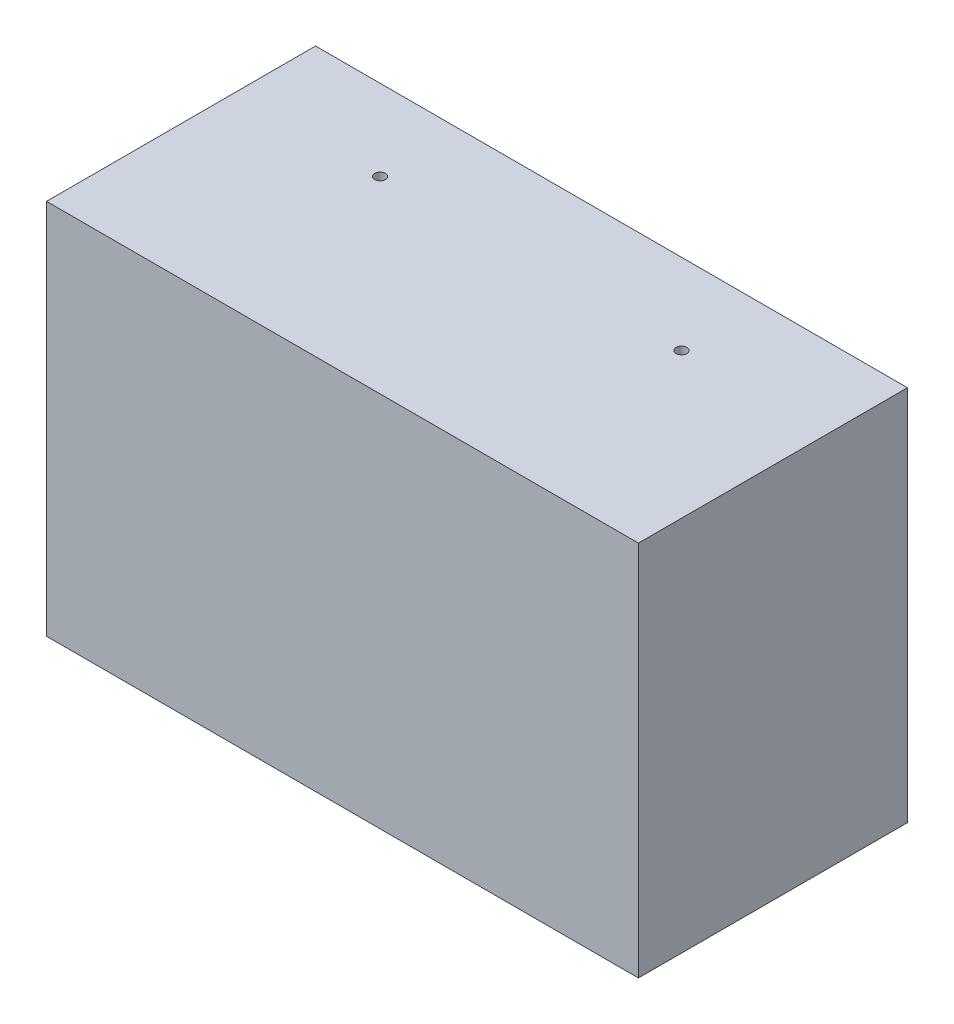
SolidWorks part; units mm, degrees
ref_plane "前基準面" through (0, 0, 0) normal (0, 0, 1) x (1, 0, 0)
ref_plane "上基準面" through (0, 0, 0) normal (0, 1, 0) x (1, 0, 0)
ref_plane "右基準面" through (0, 0, 0) normal (1, 0, 0) x (0, 0, -1)
sketch "草圖1" plane through (0, 0, 0) normal (0, 0, 1) x (1, 0, 0)
  line L0 (-102.947, 0) -> (115.7948, 0) construction
  line L1 (0, 64.9755) -> (0, -71.8056) construction
  line L3 (-55, 35) -> (55, 35)
  line L4 (-55, 35) -> (-55, -35)
  line L5 (-55, -35) -> (55, -35)
  line L6 (55, 35) -> (55, -35)
  dimension "D1" = 110
  dimension "D2" = 70
  dimension "D3" = 35
  dimension "D4" = 55
extrude "填料-伸長1" add sketch "草圖1" along normal blind 50
sketch "草圖3" plane through (0, 0, 0) normal (0, 0, 1) x (1, 0, 0)
  line L0 (0, 43.0067) -> (0, -45.1363) construction
  line L1 (63.4157, 0) -> (-65.1903, 0) construction
  line L3 (50, 30) -> (-50, 30)
  line L4 (50, 30) -> (50, -30)
  line L5 (50, -30) -> (-50, -30)
  line L6 (-50, 30) -> (-50, -30)
  dimension "D1" = 100
  dimension "D2" = 60
  dimension "D3" = 30
  dimension "D4" = 50
extrude "除料-伸長1" cut sketch "草圖3" along normal blind 35
sketch "草圖4" plane through (0, 0, 0) normal (0, 1, 0) x (1, 0, 0)
  line L0 (0, -68.6198) -> (0, 19.6124) construction
  line L1 (-69.152, -24.5037) -> (67.9388, -24.5037) construction
  line L2 (55, -50) -> (55, 0) construction
  line L3 (55, 0) -> (-55, 0) construction
  circle A0 centre (28, -15) radius 1
  circle A1 centre (-28, -15) radius 1
  dimension "D2" = 2
  dimension "D1" = 27
  dimension "D3" = 15
extrude "除料-伸長2" cut sketch "草圖4" against normal blind 40 and the other way blind 40
